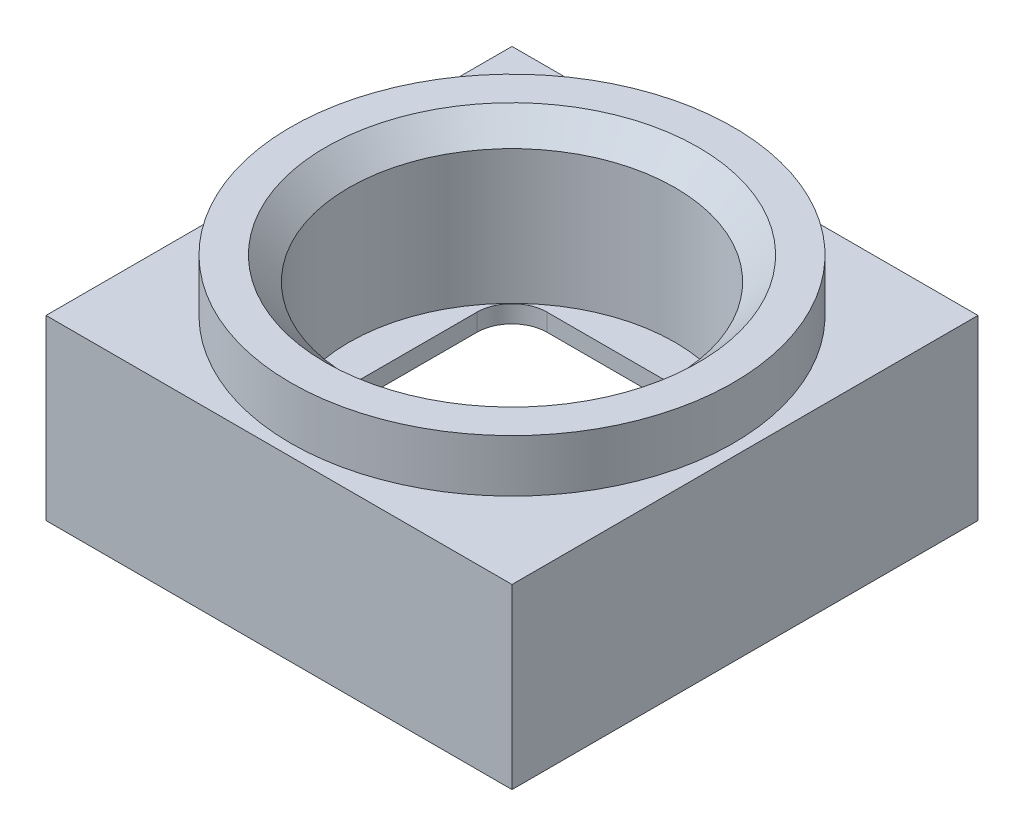
SolidWorks part; units mm, degrees
material "ABS PC"
ref_plane "Vorne" through (0, 0, 0) normal (0, 0, 1) x (1, 0, 0)
ref_plane "Oben" through (0, 0, 0) normal (0, 1, 0) x (1, 0, 0)
ref_plane "Rechts" through (0, 0, 0) normal (1, 0, 0) x (0, 0, -1)
sketch "downside" plane through (0, 0, 0) normal (0, 1, 0) x (1, 0, 0)
  line L0 (-4, 4) -> (4, -4) construction
  line L1 (-4, 4) -> (4, 4) construction
  line L2 (-4, 4) -> (-4, -4) construction
  line L3 (-4, -4) -> (4, -4) construction
  line L4 (4, 4) -> (4, -4) construction
sketch "Skizze2" plane through (0, 0, 0) normal (0, 1, 0) x (1, 0, 0)
  line L0 (-4, 4) -> (4, 4) construction
  line L1 (-4, 4) -> (-4, -4) construction
  line L2 (4, 4) -> (4, -4) construction
  line L3 (-4, -4) -> (4, -4) construction
  line L4 (-4, 4) -> (4, 4)
  line L5 (-4, 4) -> (-4, -4)
  line L6 (4, 4) -> (4, -4)
  line L7 (-4, -4) -> (4, -4)
  line L8 (-3.7, 3.7) -> (3.7, 3.7)
  line L9 (3.7, 3.7) -> (3.7, -3.7)
  line L10 (-3.7, -3.7) -> (3.7, -3.7)
  line L11 (-3.7, 3.7) -> (-3.7, -3.7)
extrude "Aufsatz-Linear austragen1" add sketch "Skizze2" along normal blind 0.6
sketch "Skizze5" plane through (0, 0.6, 0) normal (0, 1, 0) x (1, 0, 0)
  line L0 (0, 0) -> (0, 3.2) construction
  line L1 (-2.7646, 3.2) -> (2.7646, 3.2)
  line L2 (-2.7646, -3.2) -> (2.7646, -3.2)
  line L3 (-3.2, 2.7646) -> (-3.2, -2.7646)
  line L4 (3.2, 2.7646) -> (3.2, -2.7646)
  line L5 (0, 0) -> (3.2, 0) construction
  line L11 (-4, 4) -> (-4, -4)
  line L12 (-4, -4) -> (4, -4)
  line L13 (4, -4) -> (4, 4)
  line L14 (4, 4) -> (-4, 4)
  line L15 (-4, 4) -> (-4, -4)
  line L16 (-4, -4) -> (4, -4)
  line L17 (4, -4) -> (4, 4)
  line L18 (4, 4) -> (-4, 4)
  arc A0 (3.2, 2.7646) -> (2.7646, 3.2) centre (3.1, 3.1) ccw
  arc A1 (3.2, -2.7646) -> (2.7646, -3.2) centre (3.1, -3.1) cw
  arc A2 (-3.2, -2.7646) -> (-2.7646, -3.2) centre (-3.1, -3.1) ccw
  arc A3 (-3.2, 2.7646) -> (-2.7646, 3.2) centre (-3.1, 3.1) cw
  point P17 (0, -3.2)
extrude "Aufsatz-Linear austragen3" add sketch "Skizze5" along normal blind 0.35
sketch "Skizze4" plane through (0, 0.95, 0) normal (0, 1, 0) x (1, 0, 0)
  line L0 (0, 2.15) -> (0, -2.15) construction
  line L1 (-1.55, 2.15) -> (1.55, 2.15)
  line L2 (-2.15, 1.55) -> (-2.15, -1.55)
  line L3 (-1.55, -2.15) -> (1.55, -2.15)
  line L4 (2.15, 1.55) -> (2.15, -1.55)
  line L9 (4, 4) -> (-4, 4)
  line L10 (-4, 4) -> (-4, -4)
  line L11 (-4, -4) -> (4, -4)
  line L12 (4, -4) -> (4, 4)
  line L13 (4, 4) -> (-4, 4)
  line L14 (-4, 4) -> (-4, -4)
  line L15 (-4, -4) -> (4, -4)
  line L16 (4, -4) -> (4, 4)
  arc A0 (-2.15, -1.55) -> (-1.55, -2.15) centre (-1.55, -1.55) ccw
  arc A1 (1.55, -2.15) -> (2.15, -1.55) centre (1.55, -1.55) ccw
  arc A2 (1.55, 2.15) -> (2.15, 1.55) centre (1.55, 1.55) cw
  arc A3 (-1.55, 2.15) -> (-2.15, 1.55) centre (-1.55, 1.55) ccw
extrude "Aufsatz-Linear austragen2" add sketch "Skizze4" along normal blind 0.3
sketch "Skizze7" plane through (0, 1.25, 0) normal (0, 1, 0) x (1, 0, 0)
  line L4 (4, -4) -> (4, 4)
  line L5 (4, 4) -> (-4, 4)
  line L6 (-4, 4) -> (-4, -4)
  line L7 (-4, -4) -> (4, -4)
  line L8 (4, -4) -> (4, 4)
  line L9 (4, 4) -> (-4, 4)
  line L10 (-4, 4) -> (-4, -4)
  line L11 (-4, -4) -> (4, -4)
  circle A0 centre (0, 0) radius 2.8
extrude "Aufsatz-Linear austragen4" add sketch "Skizze7" along normal blind 1.8
cosmetic thread "Gewindedarstellung1"
sketch "Skizze8" plane through (0, 3.05, 0) normal (0, 1, 0) x (1, 0, 0)
  circle A0 centre (0, 0) radius 3.8
  circle A1 centre (0, 0) radius 2.8 construction
  circle A2 centre (0, 0) radius 2.8
extrude "Aufsatz-Linear austragen5" add sketch "Skizze8" along normal blind 0.9
chamfer "Fase1" distance 0.4 angle 45 1 edges at (0, 3.95, 2.8)
